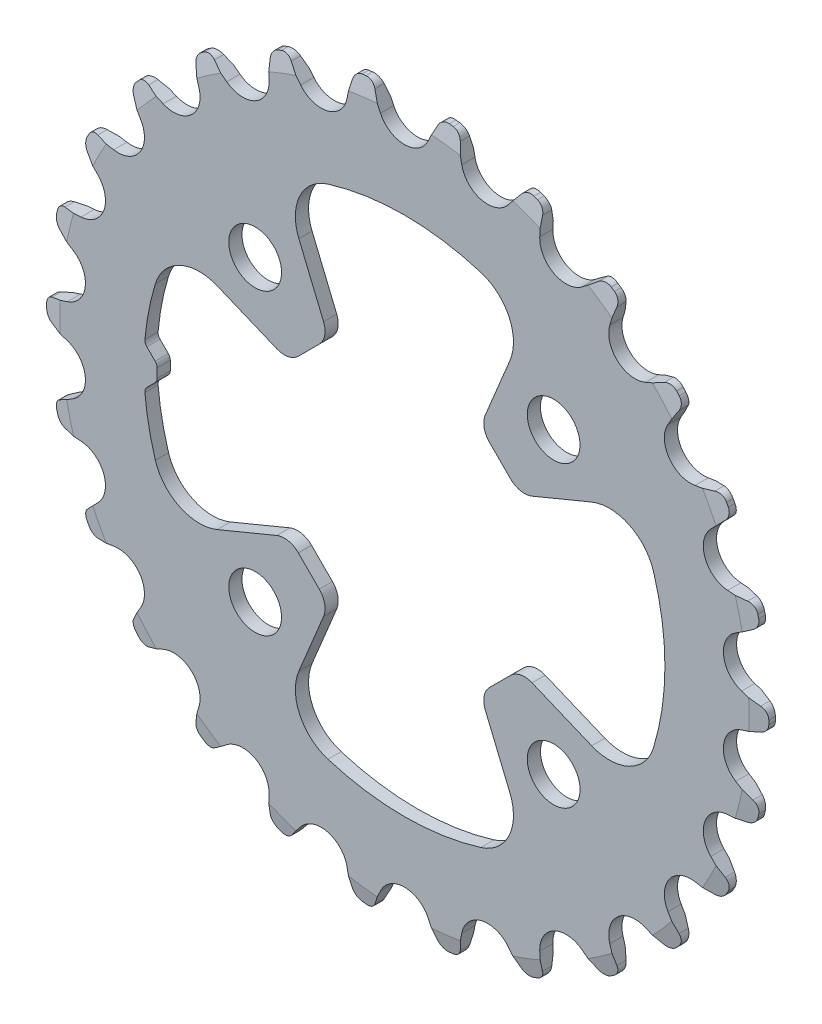
SolidWorks part; units mm, degrees
ref_plane "Plan de face" through (0, 0, 0) normal (0, 0, 1) x (1, 0, 0)
ref_plane "Plan de dessus" through (0, 0, 0) normal (0, 1, 0) x (1, 0, 0)
ref_plane "Plan de droite" through (0, 0, 0) normal (1, 0, 0) x (0, 0, -1)
sketch "Esquisse1" plane through (0, 0, 0) normal (0, 0, 1) x (1, 0, 0)
  circle A0 centre (0, 0) radius 54.75
  dimension "D1" = 109.5
extrude "Extrusion1" add sketch "Esquisse1" along normal mid plane 2
sketch "Esquisse4" plane through (0, 0, 0) normal (1, 0, 0) x (0, 0, -1)
  line L0 (-6.7593, 0) -> (13.1966, 0) construction
  line L1 (-1, 54.75) -> (-0.5, 54.75)
  line L2 (-0.5, 54.75) -> (-1, 52.25)
  line L3 (-1, 54.75) -> (-1, -54.75) construction
  line L4 (-1, 52.25) -> (-1, 54.75)
  line L5 (0, 0) -> (0, 63.6893) construction
  line L6 (1, 54.75) -> (0.5, 54.75)
  line L7 (0.5, 54.75) -> (1, 52.25)
  line L8 (1, 52.25) -> (1, 54.75)
  dimension "D1" = 2.5
  dimension "D2" = 1
revolve "Enlèvement de matière-Révolution1" cut sketch "Esquisse4" angle 360 about L0
sketch "Esquisse2" plane through (0, 0, 0) normal (0, 0, 1) x (1, 0, 0)
  line L0 (0, 0) -> (0, 69.4312) construction
  line L1 (-4.7769, 53.5292) -> (-3.6252, 51.0595)
  line L2 (4.7769, 53.5292) -> (3.6252, 51.0595)
  line L3 (0, 0) -> (87.6932, 0) construction
  arc A0 (-3.6252, 51.0595) -> (3.6252, 51.0595) centre (0, 52.75) ccw
  arc A1 (-4.7769, 53.5292) -> (-6.3092, 54.3853) centre (-6.1363, 52.8953) ccw
  arc A2 (6.3092, 54.3853) -> (-6.3092, 54.3853) centre (0, 0) ccw
  circle A3 centre (0, 0) radius 54.75 construction
  arc A4 (4.7769, 53.5292) -> (6.3092, 54.3853) centre (6.1363, 52.8953) cw
  dimension "D1" = 8
  dimension "D3" = 2
  dimension "D4" = 1.5
  dimension "D2" = 25
extrude "Enlèv. mat.-Extru.1" cut sketch "Esquisse2" against normal through all and the other way through all
pattern_circular "Répétition circulaire1" count 26 every 13.846 about axis through (0, 0, 0) along (0, 0, 1) of "Enlèv. mat.-Extru.1"
sketch "Esquisse5" plane through (0, 0, 0) normal (0, 0, 1) x (1, 0, 0)
  line L0 (0, 0) -> (40.1862, 0) construction
  line L1 (0, 0) -> (0, 40.1862) construction
  line L2 (0, 0) -> (-30.8656, 30.8656) construction
  line L3 (0, 0) -> (30.8656, 30.8656) construction
  circle A0 centre (0, 0) radius 32 construction
  circle A1 centre (-22.6274, 22.6274) radius 4
  circle A2 centre (22.6274, 22.6274) radius 4
  circle A3 centre (-22.6274, -22.6274) radius 4
  circle A4 centre (22.6274, -22.6274) radius 4
  dimension "D1" = 64
  dimension "D2" = 8
  dimension "D3" = 90
extrude "Enlèv. mat.-Extru.2" cut sketch "Esquisse5" against normal through all and the other way through all
sketch "Esquisse6" plane through (0, 0, 0) normal (0, 0, 1) x (1, 0, 0)
  line L0 (0, 0) -> (59.7996, 0) construction
  line L1 (0, 0) -> (0, 60.4392) construction
  line L2 (0, 0) -> (50.9657, 50.9657) construction
  line L3 (12.9079, 16.0835) -> (16.0835, 12.9079)
  line L4 (12.2576, 19.3528) -> (16.0014, 28.3913)
  line L5 (19.3528, 12.2576) -> (28.3913, 16.0014)
  line L6 (19.3528, -12.2576) -> (28.3913, -16.0014)
  line L7 (12.9079, -16.0835) -> (16.0835, -12.9079)
  line L8 (12.2576, -19.3528) -> (16.0014, -28.3913)
  line L9 (-12.2576, -19.3528) -> (-16.0014, -28.3913)
  line L10 (-19.3528, -12.2576) -> (-28.3913, -16.0014)
  line L11 (-19.3528, 12.2576) -> (-28.3913, 16.0014)
  line L12 (-12.2576, 19.3528) -> (-16.0014, 28.3913)
  line L13 (-12.9079, 16.0835) -> (-16.0835, 12.9079)
  line L14 (-12.9079, -16.0835) -> (-16.0835, -12.9079)
  line L15 (0, 0) -> (-68.7238, 0) construction
  line L16 (-37.7929, 1.407) -> (-39.0585, 2.6726)
  line L17 (-37.7929, -1.407) -> (-39.0585, -2.6726)
  line L18 (-37.5, 0.6999) -> (-37.5, -0.6999)
  arc A0 (-11.5878, -37.7621) -> (11.5878, -37.7621) centre (0, 0) ccw
  arc A1 (11.5878, 37.7621) -> (-11.5878, 37.7621) centre (0, 0) ccw
  arc A2 (-37.7621, 11.5878) -> (-39.3475, 3.4675) centre (0, 0) ccw
  arc A3 (37.7621, -11.5878) -> (37.7621, 11.5878) centre (0, 0) ccw
  arc A4 (-11.5878, 37.7621) -> (-16.0014, 28.3913) centre (-9.5343, 31.07) ccw
  arc A5 (16.0014, 28.3913) -> (11.5878, 37.7621) centre (9.5343, 31.07) ccw
  arc A6 (37.7621, 11.5878) -> (28.3913, 16.0014) centre (31.07, 9.5343) ccw
  arc A7 (28.3913, -16.0014) -> (37.7621, -11.5878) centre (31.07, -9.5343) ccw
  arc A8 (11.5878, -37.7621) -> (16.0014, -28.3913) centre (9.5343, -31.07) ccw
  arc A9 (-16.0014, -28.3913) -> (-11.5878, -37.7621) centre (-9.5343, -31.07) ccw
  arc A10 (-37.7621, -11.5878) -> (-28.3913, -16.0014) centre (-31.07, -9.5343) ccw
  arc A11 (-28.3913, 16.0014) -> (-37.7621, 11.5878) centre (-31.07, 9.5343) ccw
  arc A12 (-16.0835, 12.9079) -> (-19.3528, 12.2576) centre (-18.2048, 15.0292) cw
  arc A13 (-12.2576, 19.3528) -> (-12.9079, 16.0835) centre (-15.0292, 18.2048) cw
  arc A14 (12.9079, 16.0835) -> (12.2576, 19.3528) centre (15.0292, 18.2048) cw
  arc A15 (19.3528, 12.2576) -> (16.0835, 12.9079) centre (18.2048, 15.0292) cw
  arc A16 (16.0835, -12.9079) -> (19.3528, -12.2576) centre (18.2048, -15.0292) cw
  arc A17 (12.9079, -16.0835) -> (12.2576, -19.3528) centre (15.0292, -18.2048) ccw
  arc A18 (-12.9079, -16.0835) -> (-12.2576, -19.3528) centre (-15.0292, -18.2048) cw
  arc A19 (-19.3528, -12.2576) -> (-16.0835, -12.9079) centre (-18.2048, -15.0292) cw
  arc A20 (-39.3475, -3.4675) -> (-37.7621, -11.5878) centre (0, 0) ccw
  arc A21 (-39.0585, 2.6726) -> (-39.3475, 3.4675) centre (-38.3514, 3.3797) cw
  arc A22 (-37.5, 0.6999) -> (-37.7929, 1.407) centre (-38.5, 0.6999) ccw
  arc A23 (-37.7929, -1.407) -> (-37.5, -0.6999) centre (-38.5, -0.6999) ccw
  arc A24 (-39.3475, -3.4675) -> (-39.0585, -2.6726) centre (-38.3514, -3.3797) cw
  point P24 (-18.6617, 34.8137)
  point P27 (18.6617, 34.8137)
  point P30 (34.8137, 18.6617)
  point P33 (34.8137, -18.6617)
  point P36 (18.6617, -34.8137)
  point P39 (-18.6617, -34.8137)
  point P42 (-34.8137, -18.6617)
  point P45 (-34.8137, 18.6617)
  point P48 (-17.5009, 11.4905)
  point P51 (-11.4905, 17.5009)
  point P54 (11.4905, 17.5009)
  point P57 (17.5009, 11.4905)
  point P60 (17.5009, -11.4905)
  point P63 (11.4905, -17.5009)
  point P66 (-11.4905, -17.5009)
  point P69 (-17.5009, -11.4905)
  point P77 (-39.3859, 3)
  point P80 (-37.5, 1.1141)
  point P83 (-37.5, -1.1141)
  point P86 (-39.3859, -3)
  dimension "D1" = 79
  dimension "D2" = 41
  dimension "D3" = 7
  dimension "D4" = 8.5
  dimension "D6" = 3
  dimension "D8" = 2
  dimension "D10" = 1
  dimension "D5" = 45
  dimension "D7" = 6
  dimension "D9" = 90
extrude "Enlèv. mat.-Extru.3" cut sketch "Esquisse6" against normal through all and the other way through all
